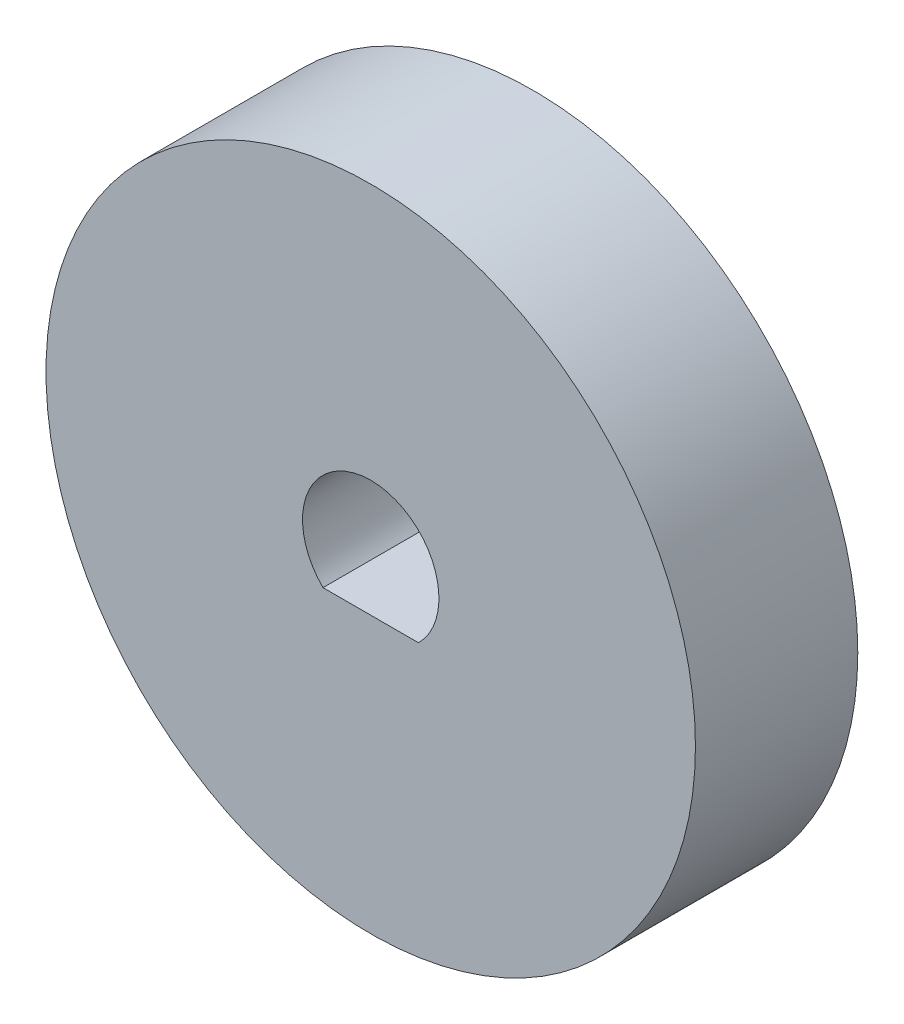
SolidWorks part; units mm, degrees
ref_plane "Спереди" through (0, 0, 0) normal (0, 0, 1) x (1, 0, 0)
ref_plane "Сверху" through (0, 0, 0) normal (0, 1, 0) x (1, 0, 0)
ref_plane "Справа" through (0, 0, 0) normal (1, 0, 0) x (0, 0, -1)
sketch "Эскиз1" plane through (0, 0, 0) normal (0, 0, 1) x (1, 0, 0)
  circle A0 centre (0, 0) radius 10
  dimension "D1" = 20
extrude "Бобышка-Вытянуть2" add sketch "Эскиз1" along normal blind 5
sketch "Эскиз3" plane through (0, 0, 5) normal (0, 0, 1) x (1, 0, 0)
  line L0 (1.4697, -1.5) -> (-1.4697, -1.5)
  arc A0 (1.4697, -1.5) -> (-1.4697, -1.5) centre (0, 0) ccw
  dimension "D1" = 4.2
  dimension "D2" = 1.5
extrude "Вырез-Вытянуть1" cut sketch "Эскиз3" against normal blind 5
